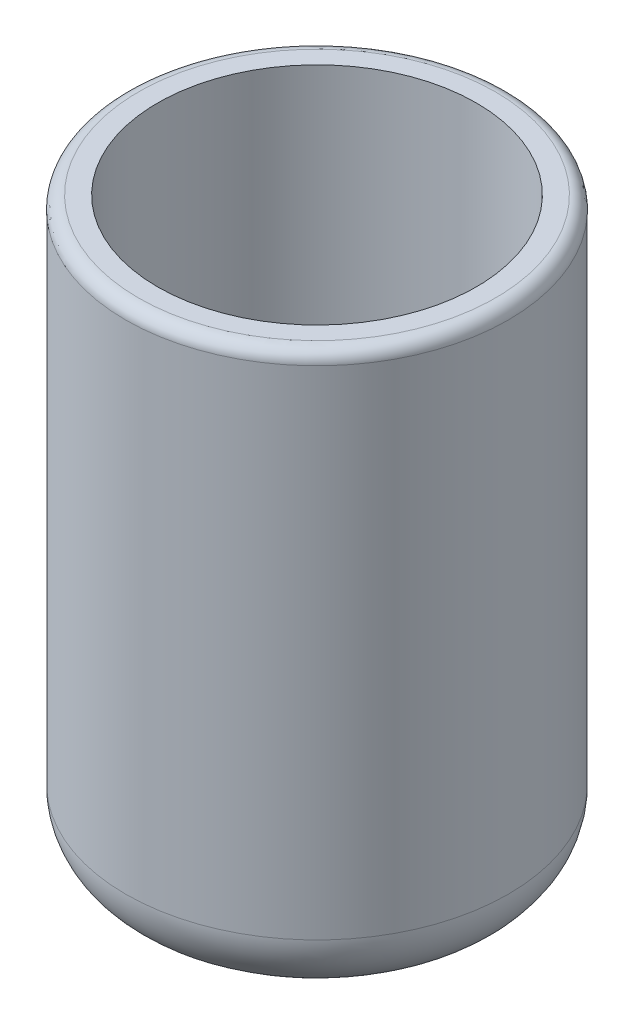
SolidWorks part; units mm, degrees
ref_plane "Alzado" through (0, 0, 0) normal (0, 0, 1) x (1, 0, 0)
ref_plane "Planta" through (0, 0, 0) normal (0, 1, 0) x (1, 0, 0)
ref_plane "Vista lateral" through (0, 0, 0) normal (1, 0, 0) x (0, 0, -1)
sketch "Croquis2" plane through (0, 0, 0) normal (0, 1, 0) x (1, 0, 0)
  circle A0 centre (0, 0) radius 1.5
  dimension "D1" = 3
extrude "Saliente-Extruir1" add sketch "Croquis2" along normal blind 4.5
shell "Vaciado1" thickness 0.25
fillet "Redondeo1" radius 0.1 1 edges at (0, 4.5, 1.5)
fillet "Redondeo2" radius 0.5 1 edges at (0, 0, 1.5)
